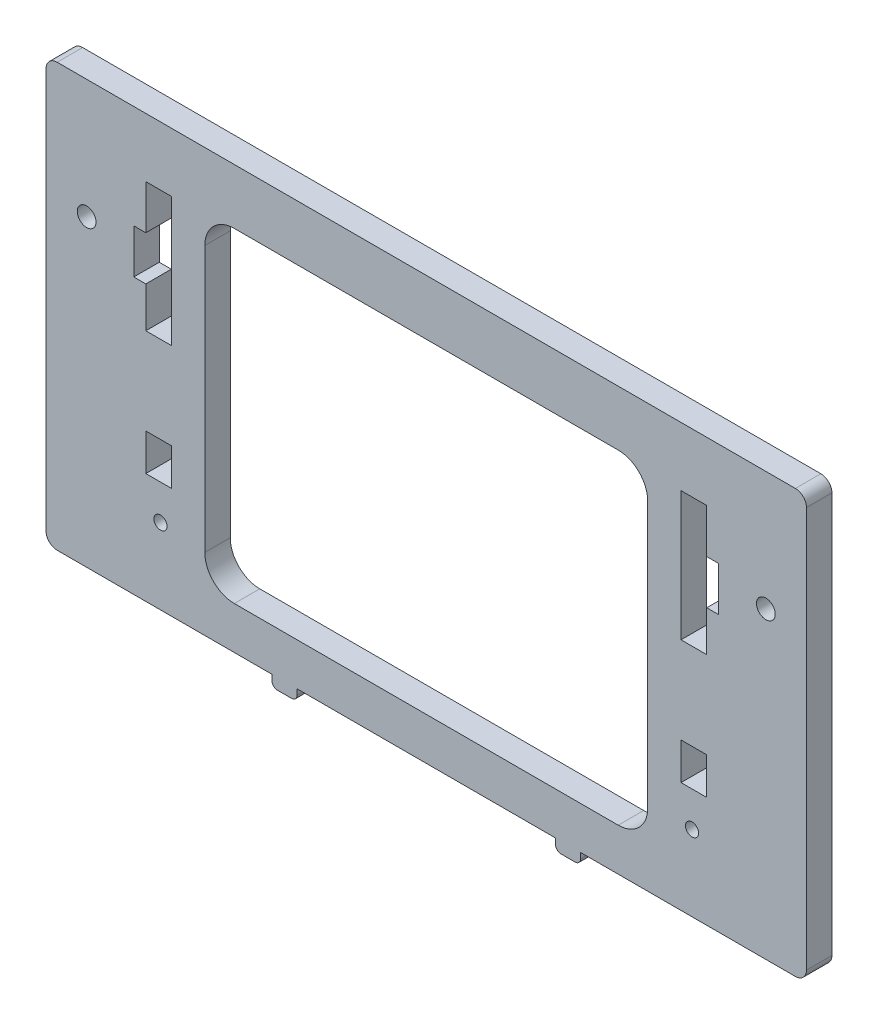
SolidWorks part; units mm, degrees
ref_plane "Front Plane" through (0, 0, 0) normal (0, 0, 1) x (1, 0, 0)
ref_plane "Top Plane" through (0, 0, 0) normal (0, 1, 0) x (1, 0, 0)
ref_plane "Right Plane" through (0, 0, 0) normal (1, 0, 0) x (0, 0, -1)
sketch "Sketch1" plane through (0, 0, 0) normal (0, 0, 1) x (1, 0, 0)
  line L1 (103, 57.25) -> (-103, 57.25)
  line L2 (103, 57.25) -> (103, -57.25)
  line L3 (103, -57.25) -> (-103, -57.25)
  line L4 (-103, 57.25) -> (-103, -57.25)
  line L5 (103, 57.25) -> (-103, -57.25) construction
  line L6 (103, -57.25) -> (-103, 57.25) construction
  point P0 (0, 0)
  dimension "D1" = 114.5
  dimension "D2" = 206
extrude "Boss-Extrude1" add sketch "Sketch1" against normal blind 6.9
sketch "Sketch2" plane through (0, 0, 0) normal (0, 0, 1) x (1, 0, 0)
  line L0 (103, 57.25) -> (-103, 57.25) construction
  line L1 (60, -45.75) -> (-60, -45.75)
  line L2 (60, -45.75) -> (60, 42.25)
  line L3 (60, 42.25) -> (-60, 42.25)
  line L4 (-60, -45.75) -> (-60, 42.25)
  line L5 (60, -45.75) -> (-60, 42.25) construction
  line L6 (60, 42.25) -> (-60, -45.75) construction
  point P0 (0, -1.75)
  dimension "D1" = 15
  dimension "D2" = 88
  dimension "D3" = 120
extrude "Cut-Extrude1" cut sketch "Sketch2" against normal through all
fillet "Fillet1" radius 8 4 edges at (60, 42.25, -3.45) (60, -45.75, -3.45) (-60, -45.75, -3.45) (-60, 42.25, -3.45)
sketch "Sketch3" plane through (0, 0, 0) normal (0, 0, 1) x (1, 0, 0)
  line L0 (103, 57.25) -> (-103, 57.25) construction
  line L1 (-91.775, 78.25) -> (-88.225, 78.25)
  line L2 (-91.775, 78.25) -> (-91.775, 36.25)
  line L3 (-91.775, 36.25) -> (-88.225, 36.25)
  line L4 (-88.225, 78.25) -> (-88.225, 36.25)
  line L5 (-91.775, 78.25) -> (-88.225, 36.25) construction
  line L6 (-91.775, 36.25) -> (-88.225, 78.25) construction
  point P0 (-90, 57.25)
  dimension "D1" = 3.55
  dimension "D2" = 21
  dimension "D3" = 90
extrude "Cut-Extrude2" [suppressed] cut sketch "Sketch3" against normal through all
sketch "Sketch4" plane through (0, 0, 0) normal (0, 0, 1) x (1, 0, 0)
  line L0 (103, 57.25) -> (-103, 57.25) construction
  line L1 (-93.81, 46.25) -> (-86.19, 46.25)
  line L2 (-93.81, 46.25) -> (-93.81, 41.25)
  line L3 (-93.81, 41.25) -> (-86.19, 41.25)
  line L4 (-86.19, 46.25) -> (-86.19, 41.25)
  line L5 (-93.81, 46.25) -> (-86.19, 41.25) construction
  line L6 (-93.81, 41.25) -> (-86.19, 46.25) construction
  point P0 (-90, 43.75)
  dimension "D1" = 7.62
  dimension "D2" = 5
  dimension "D3" = 11
extrude "Cut-Extrude3" [suppressed] cut sketch "Sketch4" against normal through all
sketch "Sketch5" plane through (0, 0, 0) normal (0, 0, 1) x (1, 0, 0)
  line L0 (103, 57.25) -> (-103, 57.25) construction
  line L1 (-65, 57.25) -> (-50, 57.25)
  line L2 (-65, 57.25) -> (-65, 63.75)
  line L3 (-65, 63.75) -> (-50, 63.75)
  line L4 (-50, 57.25) -> (-50, 63.75)
  line L7 (0, 57.25) -> (-7.5, 57.25)
  line L8 (0, 57.25) -> (0, 63.75)
  line L9 (0, 63.75) -> (-7.5, 63.75)
  line L10 (-7.5, 57.25) -> (-7.5, 63.75)
  dimension "D1" = 6.5
  dimension "D2" = 15
  dimension "D3" = 57.5
  dimension "D4" = 7.5
extrude "Boss-Extrude2" [suppressed] add sketch "Sketch5" against normal up to surface (6.9 mm away)
mirror "Mirror1" [suppressed] about plane through (0, 0, 0) normal (0, 1, 0)
sketch "Sketch7" plane through (0, 0, 0) normal (0, 0, 1) x (1, 0, 0)
  line L0 (-92, 25) -> (-92, -25) construction
  line L1 (-92, 0) -> (0, 0) construction
  circle A0 centre (-92, 25) radius 2.54
  circle A1 centre (-92, -25) radius 2.54 construction
  dimension "D3" = 5.08
  dimension "D1" = 92
  dimension "D2" = 50
extrude "Cut-Extrude5" cut sketch "Sketch7" against normal through all
sketch "Sketch9" plane through (0, 0, 0) normal (0, 0, 1) x (1, 0, 0)
  line L1 (-75.98, 41.25) -> (-69.02, 41.25)
  line L2 (-75.98, 41.25) -> (-75.98, 6.25)
  line L3 (-75.98, 6.25) -> (-69.02, 6.25)
  line L4 (-69.02, 41.25) -> (-69.02, 6.25)
  line L5 (-75.98, 41.25) -> (-69.02, 6.25) construction
  line L6 (-75.98, 6.25) -> (-69.02, 41.25) construction
  line L7 (-103, -57.25) -> (103, -57.25) construction
  line L8 (-75.98, -17.25) -> (-69.02, -17.25)
  line L9 (-75.98, -17.25) -> (-75.98, -27.25)
  line L10 (-75.98, -27.25) -> (-69.02, -27.25)
  line L11 (-69.02, -17.25) -> (-69.02, -27.25)
  line L12 (-75.98, -17.25) -> (-69.02, -27.25) construction
  line L13 (-75.98, -27.25) -> (-69.02, -17.25) construction
  point P0 (-72.5, 23.75)
  point P8 (-72.5, -22.25)
  dimension "D1" = 35
  dimension "D2" = 6.96
  dimension "D3" = 72.5
  dimension "D4" = 68.5
  dimension "D5" = 10
  dimension "D6" = 30
extrude "Cut-Extrude7" cut sketch "Sketch9" against normal through all
sketch "Sketch11" plane through (0, 0, 0) normal (0, 0, 1) x (1, 0, 0)
  line L0 (-75.98, 41.25) -> (-75.98, 6.25) construction
  line L1 (-75.98, 29.25) -> (-79.23, 29.25)
  line L2 (-75.98, 29.25) -> (-75.98, 17.25)
  line L3 (-75.98, 17.25) -> (-79.23, 17.25)
  line L4 (-79.23, 29.25) -> (-79.23, 17.25)
  line L5 (-69.02, 41.25) -> (-75.98, 41.25) construction
  point P6 (-72.5, 41.25)
  dimension "D1" = 3.25
  dimension "D2" = 12
  dimension "D3" = 12
extrude "Cut-Extrude8" cut sketch "Sketch11" against normal through all
mirror "Mirror2" about plane through (0, 0, 0) normal (1, 0, 0) of "Cut-Extrude8", "Cut-Extrude5", "Cut-Extrude7"
fillet "Fillet2" radius 3 4 edges at (103, 57.25, -3.45) (103, -57.25, -3.45) (-103, -57.25, -3.45) (-103, 57.25, -3.45)
sketch "Sketch8" plane through (0, 0, 0) normal (0, 0, 1) x (1, 0, 0)
  line L0 (-72, -36.75) -> (72, -36.75) construction
  line L1 (-100, -57.25) -> (100, -57.25) construction
  circle A0 centre (72, -36.75) radius 1.775
  circle A1 centre (-72, -36.75) radius 1.775
  point P4 (0, -36.75)
  dimension "D1" = 3.55
  dimension "D2" = 144
  dimension "D3" = 20.5
extrude "Cut-Extrude6" cut sketch "Sketch8" against normal through all
sketch "Sketch10" plane through (0, 0, 0) normal (0, 0, 1) x (1, 0, 0)
  line L0 (-100, -57.25) -> (100, -57.25) construction
  line L1 (-41.8, -57.25) -> (-35, -57.25)
  line L2 (-41.8, -57.25) -> (-41.8, -60.25)
  line L3 (-41.8, -60.25) -> (-35, -60.25)
  line L4 (-35, -57.25) -> (-35, -60.25)
  line L5 (0, 0) -> (0, -33.8944) construction
  line L6 (35, -57.25) -> (35, -60.25)
  line L7 (41.8, -60.25) -> (35, -60.25)
  line L8 (41.8, -57.25) -> (41.8, -60.25)
  line L9 (41.8, -57.25) -> (35, -57.25)
  line L10 (-35, -57.25) -> (-35, -35.0742) construction
  dimension "D1" = 3
  dimension "D2" = 35
  dimension "D3" = 6.8
extrude "Boss-Extrude3" add sketch "Sketch10" against normal up to surface (6.9 mm away) up to face at (-70.225, -36.75, -6.9)
fillet "Fillet3" radius 1.5 4 edges at (41.8, -60.25, -3.45) (35, -60.25, -3.45) (-35, -60.25, -3.45) (-41.8, -60.25, -3.45)
sketch "Sketch12" plane through (0, 0, 0) normal (0, 0, 1) x (1, 0, 0)
  text T0 "SeeMeCNC  87912  R1" font "1CamBam_Stick_9" height 2.5
